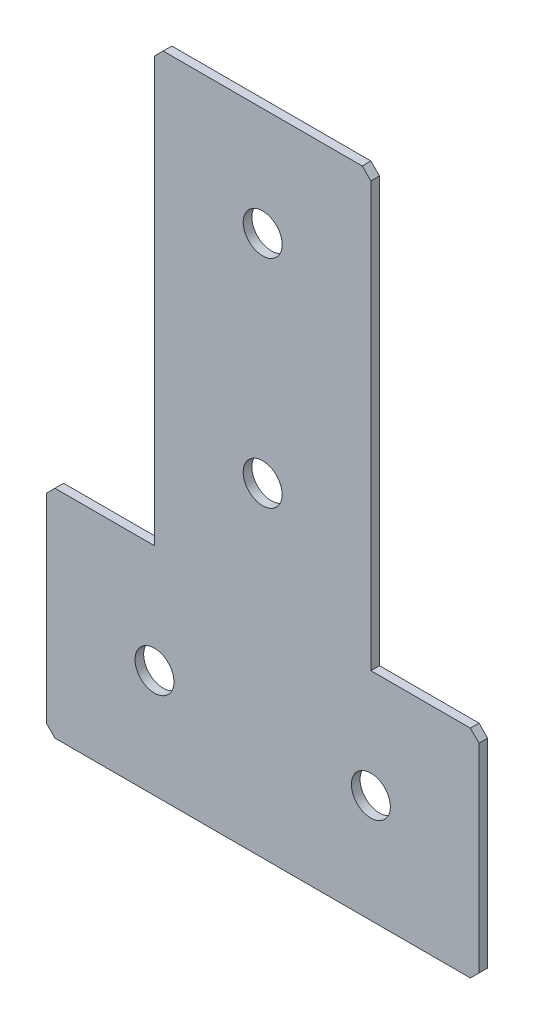
SolidWorks part; units mm, degrees
material "Простая углеродистая сталь"
ref_plane "Спереди(Плоскость XY)" through (0, 0, 0) normal (0, 0, 1) x (1, 0, 0)
ref_plane "Сверху(Плоскость XZ)" through (0, 0, 0) normal (0, 1, 0) x (1, 0, 0)
ref_plane "Справа(Плоскость ZY)" through (0, 0, 0) normal (1, 0, 0) x (0, 0, -1)
sketch "Эскиз1" plane through (0, 0, 0) normal (0, 0, -1) x (1, 0, 0)
  line L0 (0, 0) -> (0, 150) construction
  line L1 (-50, 150) -> (50, 150)
  line L2 (50, 150) -> (50, 100)
  line L3 (50, 100) -> (25, 100)
  line L4 (25, 100) -> (25, 0)
  line L5 (25, 0) -> (-25, 0)
  line L6 (-50, 150) -> (-50, 100)
  line L7 (-50, 100) -> (-25, 100)
  line L8 (-25, 100) -> (-25, 0)
  line L10 (-50, 125) -> (50, 125) construction
  dimension "D1" = 150
  dimension "D2" = 100
  dimension "D3" = 50
extrude "Бобышка-Вытянуть1" add sketch "Эскиз1" along normal blind 2
hole_wizard "Отверстие с зазором M81" positions "Эскиз2" profile "Эскиз3" hole size "M8" standard "DIN" end condition through all
sketch "Эскиз2" plane through (0, 0, -2) normal (0, 0, -1) x (1, 0, 0)
  line L6 (0, 0) -> (0, 125) construction
  line L12 (-25, 125) -> (25, 125) construction
  line L14 (25, 125) -> (50, 125) construction
  line L15 (50, 100) -> (50, 150) construction
  line L17 (-25, 0) -> (25, 0) construction
  point P40 (-25, 125)
  point P42 (25, 125)
  point P44 (0, 75)
  point P46 (0, 25)
  dimension "D1" = 50
  dimension "D2" = 25
  dimension "D3" = 50
sketch "Эскиз3" plane through (0, -25, -2) normal (1, 0, 0) x (0, 1, 0)
  line L0 (0, 0) -> (0, 2)
  line L1 (0, 2) -> (4.5, 2)
  line L2 (4.5, 2) -> (4.5, 0)
  line L5 (4.5, 0) -> (0, 0)
  line L11 (0, -6.35) -> (0, 107.95) construction
  dimension "Диаметр сквозного отверстия" = 9
  dimension "Глубина сквозного отверстия" = 2
chamfer "Фаска1" distance 2 angle 45 6 edges at (25, 0, -1) (50, -100, -1) (50, -150, -1) (-50, -150, -1) (-50, -100, -1) (-25, 0, -1)
